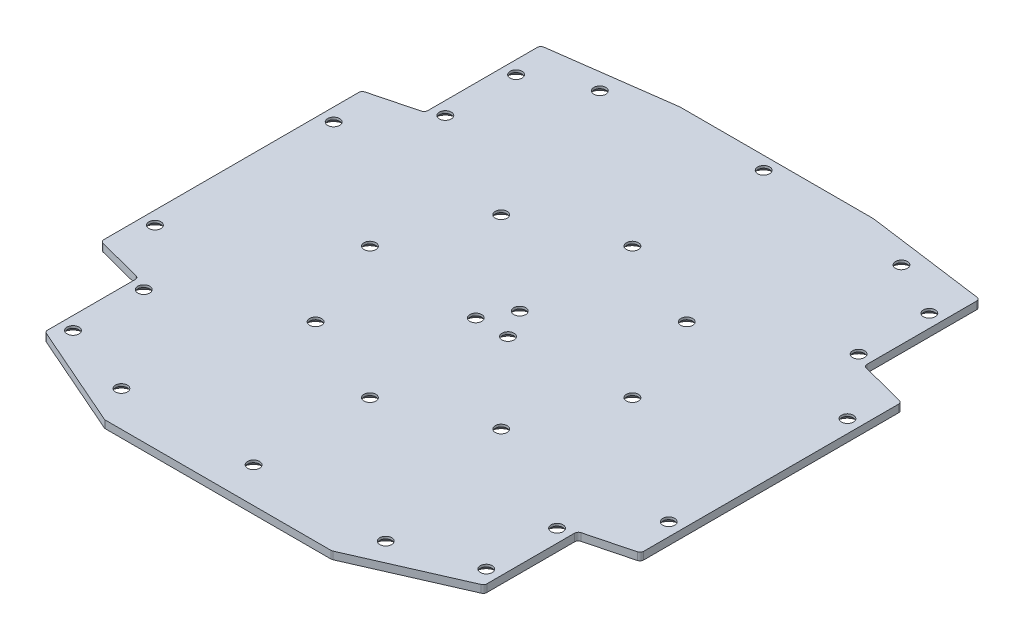
SolidWorks part; units mm, degrees
material "7075-T6, Plate (SS)"
ref_plane "Front Plane" through (0, 0, 0) normal (0, 0, 1) x (1, 0, 0)
ref_plane "Top Plane" through (0, 0, 0) normal (0, 1, 0) x (1, 0, 0)
ref_plane "Right Plane" through (0, 0, 0) normal (1, 0, 0) x (0, 0, -1)
sketch "Sketch1" plane through (0, 0, 0) normal (0, 1, 0) x (1, 0, 0)
  line L0 (0, 74) -> (0, 0) construction
  line L1 (-80.5, -76) -> (80.5, -76)
  line L2 (-80.5, -76) -> (-80.5, 74)
  line L3 (-80.5, 74) -> (80.5, 74)
  line L4 (80.5, -76) -> (80.5, 74)
  line L7 (-74.5, 38.5) -> (-59, 38.5)
  line L8 (-74.5, 38.5) -> (-74.5, 61.5)
  line L9 (-74.5, 61.5) -> (-59, 61.5)
  line L10 (-59, 38.5) -> (-59, 61.5)
  line L11 (0, 0) -> (60.5471, 0) construction
  line L12 (59, 38.5) -> (59, 61.5)
  line L13 (74.5, 61.5) -> (59, 61.5)
  line L14 (74.5, 38.5) -> (74.5, 61.5)
  line L15 (74.5, 38.5) -> (59, 38.5)
  line L16 (74.5, -38.5) -> (59, -38.5)
  line L17 (74.5, -38.5) -> (74.5, -61.5)
  line L18 (74.5, -61.5) -> (59, -61.5)
  line L19 (59, -38.5) -> (59, -61.5)
  line L20 (-59, -38.5) -> (-59, -61.5)
  line L21 (-74.5, -61.5) -> (-59, -61.5)
  line L22 (-74.5, -38.5) -> (-74.5, -61.5)
  line L23 (-74.5, -38.5) -> (-59, -38.5)
  point P0 (0, 0)
  point P25 (-59, 50)
  point P26 (0, 74)
  dimension "D1" = 74
  dimension "D2" = 161
  dimension "D3" = 23
  dimension "D4" = 15.5
  dimension "D5" = 50
  dimension "D6" = 59
  dimension "D7" = 76
extrude "Boss-Extrude1" add sketch "Sketch1" along normal blind 2.032
hole_wizard "CSK for M3 SFHCS1" positions "Sketch3" profile "Sketch2" countersink size "M3" standard "ANSI Metric" end condition through all
sketch "Sketch3" plane through (0, 0, 0) normal (0, -1, 0) x (-1, 0, 0)
  point P0 (0, -35.25)
  point P8 (-24.9255, -24.9255)
  point P9 (-35.25, 0)
  point P10 (-24.9255, 24.9255)
  point P11 (0, 35.25)
  point P12 (24.9255, 24.9255)
  point P13 (35.25, 0)
  point P14 (24.9255, -24.9255)
  point P15 (0, 5)
  point P51 (4.3301, -2.5)
  point P52 (-4.3301, -2.5)
  dimension "D1" = 35.25
  dimension "D3" = 35.25
  dimension "D4" = 5
  dimension "D2" = 8
  dimension "D5" = 3
sketch "Sketch2" plane through (0, 0, 35.25) normal (1, 0, 0) x (0, 0, -1)
  line L0 (0, 0) -> (0, 2.032)
  line L1 (0, 2.032) -> (1.6, 2.032)
  line L2 (1.6, 2.032) -> (1.6, 1.4)
  line L3 (1.6, 1.4) -> (3, 0)
  line L5 (3, 0) -> (0, 0)
  line L6 (-1.6, 1.4) -> (-3, 0) construction
  line L11 (0, -6.35) -> (0, 107.95) construction
  dimension "Thru Hole Dia." = 3.2
  dimension "Thru Hole Depth" = 2.032
  dimension "Near C'Sink Dia." = 6
  dimension "Near C'Sink Angle" = 90
sketch "Sketch4" plane through (0, 0, 0) normal (0, -1, 0) x (1, 0, 0)
  line L0 (59, -38.5) -> (72.5, -35)
  line L1 (72.5, -35) -> (72.5, 35)
  line L4 (80.5, 76) -> (80.5, -74) construction
  line L7 (-80.5, 76) -> (-80.5, -74)
  line L8 (80.5, -74) -> (26, -74)
  line L9 (80.5, -74) -> (-80.5, -74) construction
  line L10 (26, -74) -> (59, -69.5286)
  line L11 (59, -69.5286) -> (59, -38.5)
  line L14 (26, -74) -> (74.4399, -67.4366) construction
  line L15 (0, 0) -> (0, -58.6828) construction
  line L16 (59, -61.5) -> (59, -38.5) construction
  line L17 (72.5, 35) -> (59, 38.5)
  line L18 (59, 38.5) -> (59, 63.5)
  line L19 (59, 38.5) -> (59, 61.5) construction
  line L20 (59, 63.5) -> (30.5, 76)
  line L21 (-80.5, 76) -> (80.5, 76) construction
  line L22 (72.5, -27.8787) -> (72.5, 27.8787) construction
  line L23 (59, 61.5) -> (74.5, 61.5) construction
  line L24 (30.5, 76) -> (80.5, 76)
  line L25 (80.5, 76) -> (80.5, -74)
  line L26 (-30.5, 76) -> (-80.5, 76)
  line L27 (-59, 63.5) -> (-30.5, 76)
  line L28 (-59, 38.5) -> (-59, 63.5)
  line L29 (-72.5, 35) -> (-59, 38.5)
  line L30 (-59, -69.5286) -> (-59, -38.5)
  line L31 (-26, -74) -> (-59, -69.5286)
  line L32 (-80.5, -74) -> (-26, -74)
  line L33 (-72.5, -35) -> (-72.5, 35)
  line L34 (-59, -38.5) -> (-72.5, -35)
  point P27 (72.5, 0)
  dimension "D1" = 70
  dimension "D2" = 2
  dimension "D3" = 50
extrude "Cut-Extrude1" cut sketch "Sketch4" against normal through all
fillet "Fillet1" radius 1 16 edges at (-59, 1.016, -38.5) (-59, 1.016, -69.5286) (-26, 1.016, -74) (26, 1.016, -74) (59, 1.016, -69.5286) (59, 1.016, -38.5) (72.5, 1.016, -35) (72.5, 1.016, 35) (59, 1.016, 38.5) (59, 1.016, 63.5) (30.5, 1.016, 76) (-72.5, 1.016, 35) (-59, 1.016, 38.5) (-30.5, 1.016, 76) (-59, 1.016, 63.5) (-72.5, 1.016, -35)
hole_wizard "CSK for M3 SFHCS2" positions "Sketch6" profile "Sketch5" countersink size "M3" standard "ANSI Metric" end condition through all
sketch "Sketch6" plane through (0, 0, 0) normal (0, -1, 0) x (-1, 0, 0)
  line L1 (-14.5655, 0) -> (0, 0) construction
  line L2 (0, 0) -> (0, -26.6419) construction
  circle A0 centre (0, -66.5) radius 1.25 construction
  circle A1 centre (35.5, -66.5) radius 1.25 construction
  circle A3 centre (55.5, -59.5) radius 1.25 construction
  circle A5 centre (55.5, -40.5) radius 1.25 construction
  circle A7 centre (69, -24) radius 1.25 construction
  circle A12 centre (-40.5, 67) radius 1.25 construction
  circle A14 centre (0, 70.5) radius 1.25 construction
  point P0 (0, -66.5)
  point P2 (35.5, -66.5)
  point P8 (69, -24)
  point P14 (55.5, -40.5)
  point P18 (55.5, -59.5)
  point P60 (-55.5, -59.5)
  point P62 (-55.5, -40.5)
  point P63 (-69, -24)
  point P66 (-35.5, -66.5)
  point P68 (-69, 24)
  point P69 (-55.5, 40.5)
  point P71 (-55.5, 59.5)
  point P72 (55.5, 59.5)
  point P74 (55.5, 40.5)
  point P75 (69, 24)
  point P82 (-40.5, 67)
  point P86 (0, 70.5)
  point P101 (40.5, 67)
sketch "Sketch5" plane through (0, 0, 66.5) normal (1, 0, 0) x (0, 0, -1)
  line L0 (0, 0) -> (0, 2.032)
  line L1 (0, 2.032) -> (1.6, 2.032)
  line L2 (1.6, 2.032) -> (1.6, 1.4)
  line L3 (1.6, 1.4) -> (3, 0)
  line L5 (3, 0) -> (0, 0)
  line L6 (-1.6, 1.4) -> (-3, 0) construction
  line L11 (0, -6.35) -> (0, 107.95) construction
  dimension "Thru Hole Dia." = 3.2
  dimension "Thru Hole Depth" = 2.032
  dimension "Near C'Sink Dia." = 6
  dimension "Near C'Sink Angle" = 90
